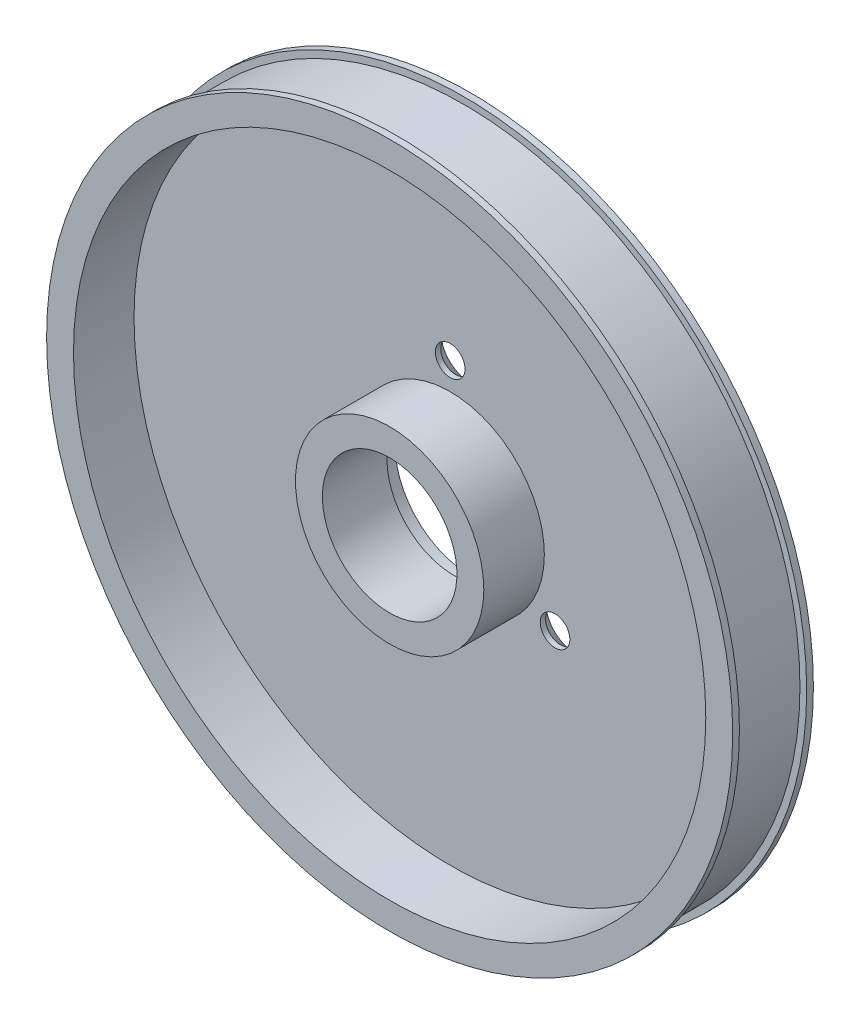
SolidWorks part; units mm, degrees
material "6061 Alloy"
ref_plane "Front Plane" through (0, 0, 0) normal (0, 0, 1) x (1, 0, 0)
ref_plane "Top Plane" through (0, 0, 0) normal (0, 1, 0) x (1, 0, 0)
ref_plane "Right Plane" through (0, 0, 0) normal (1, 0, 0) x (0, 0, -1)
sketch "Sketch1" plane through (0, 0, 0) normal (0, 1, 0) x (1, 0, 0)
  line L0 (25.5, 0) -> (0, 0)
  line L1 (0, 0) -> (0, -6)
  line L2 (0, -6) -> (25.5, -6)
  line L3 (25.5, -6) -> (25.5, -5.5)
  line L4 (25.5, -5.5) -> (25, -5.5)
  line L5 (25, -5.5) -> (25, -0.5)
  line L6 (25, -0.5) -> (25.5, -0.5)
  line L7 (25.5, -0.5) -> (25.5, 0)
  line L8 (0, 0) -> (0, -6) construction
revolve "Revolve1" add sketch "Sketch1" angle 360 about L8
hole_wizard "M42 Clearance Hole1" positions "Sketch3" profile "Sketch2" hole size "M42" standard "ANSI Metric"
sketch "Sketch3" plane through (0, 0, 6) normal (0, 0, 1) x (1, 0, 0)
  point P0 (0, 0)
sketch "Sketch2" plane through (0, 0, 6) normal (1, 0, 0) x (0, -1, 0)
  line L0 (0, 0) -> (0, 4.5)
  line L1 (0, 4.5) -> (23.5, 4.5)
  line L2 (23.5, 4.5) -> (23.5, 0)
  line L5 (23.5, 0) -> (0, 0)
  line L10 (0, 4.5) -> (-23.5, 4.5) construction
  line L11 (0, -6.35) -> (0, 107.95) construction
  dimension "Hole Dia." = 47
  dimension "Hole Depth" = 4.5
  dimension "Drill Angle" = 180
sketch "Sketch4" plane through (0, 0, 0) normal (0, 1, 0) x (1, 0, 0)
  line L0 (7, -1.5) -> (0, -1.5)
  line L1 (0, -1.5) -> (0, -6)
  line L2 (0, -6) -> (7, -6)
  line L3 (7, -6) -> (7, -1.5)
  line L4 (0, -1.5) -> (0, -6) construction
revolve "Revolve2" add sketch "Sketch4" angle 360 about L4
hole_wizard "CSK for M2 Flat Head Machine Screw1" positions "Sketch6" profile "Sketch5" countersink size "M2" standard "ANSI Metric"
sketch "Sketch6" plane through (0, 0, 0) normal (0, 0, -1) x (-1, 0, 0)
  point P0 (-7.7942, -4.5)
  point P1 (7.7942, -4.5)
  point P2 (0, 9)
sketch "Sketch5" plane through (7.7942, -4.5, 0) normal (1, 0, 0) x (0, 1, 0)
  line L0 (0, 0) -> (0, 6)
  line L1 (0, 6) -> (1.1, 6)
  line L2 (1.1, 6) -> (1.1, 1.1)
  line L3 (1.1, 1.1) -> (2.2, 0)
  line L5 (2.2, 0) -> (0, 0)
  line L6 (-1.1, 1.1) -> (-2.2, 0) construction
  line L11 (0, -6.35) -> (0, 107.95) construction
  dimension "Thru Hole Dia." = 2.2
  dimension "Thru Hole Depth" = 6
  dimension "Near C'Sink Dia." = 4.4
  dimension "Near C'Sink Angle" = 90
hole_wizard "CBORE for M8 Hex Head Bolt1" positions "Sketch8" profile "Sketch7" counterbore size "M8" standard "ANSI Metric"
sketch "Sketch8" plane through (0, 0, 0) normal (0, 0, -1) x (-1, 0, 0)
  point P0 (0, 0)
sketch "Sketch7" plane through (0, 0, 0) normal (1, 0, 0) x (0, 1, 0)
  line L0 (0, 0) -> (0, 6)
  line L1 (0, 6) -> (5, 6)
  line L3 (5, 6) -> (5, 1.2)
  line L4 (5, 1.2) -> (5.6, 1.2)
  line L5 (5.6, 1.2) -> (5.6, 0)
  line L7 (5.6, 0) -> (0, 0)
  line L11 (0, -6.35) -> (0, 107.95) construction
  dimension "Thru Hole Dia." = 10
  dimension "Thru Hole Depth" = 6
  dimension "C'Bore Dia." = 11.2
  dimension "C'Bore Depth" = 1.2
